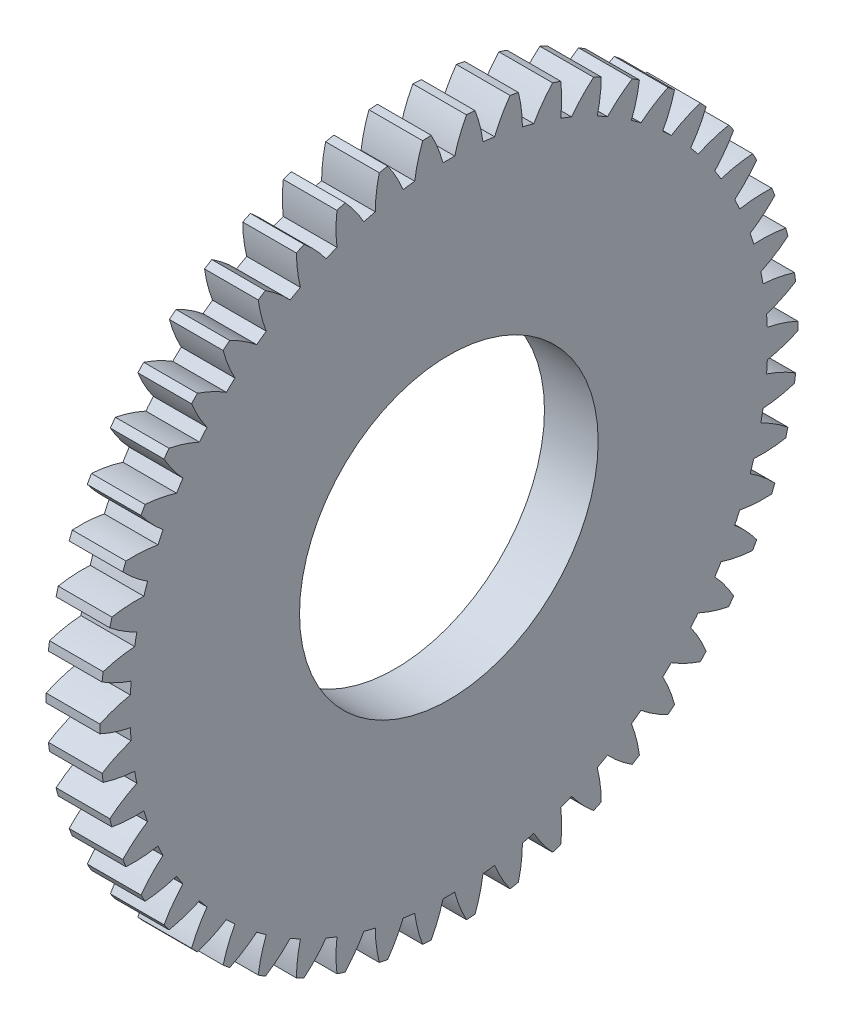
SolidWorks part; units mm, degrees
ref_plane "Plane1" through (0, 0, 0) normal (0, 0, 1) x (1, 0, 0)
ref_plane "Plane2" through (0, 0, 0) normal (0, 1, 0) x (1, 0, 0)
ref_plane "Plane3" through (0, 0, 0) normal (1, 0, 0) x (0, 0, -1)
sketch "HoldingSke" plane through (0, 0, 0) normal (0, 1, 0) x (1, 0, 0)
  line L0 (0, 0) -> (0.6428, -0.766)
  line L1 (-15, 0) -> (100, 0) construction
  line L2 (0, 0) -> (-2.1039, 2.3779)
  line L3 (0, 0) -> (-11.863, 4.5341)
  line L4 (0, 0) -> (5.5511, 6.6156)
  line L5 (0, 0) -> (-46.8476, -17.4728)
  line L6 (0, 0) -> (-3.3159, -2.2372)
  line L7 (-2.1039, 2.3779) -> (8.6586, 51.2059)
  line L8 (-76.2, 54.61) -> (-75.3, 54.61)
  line L9 (-71.009, 38.7566) -> (-53.1078, 45.2721)
  line L10 (-76.2, 71.12) -> (104.1128, 71.12)
  line L11 (0, 0) -> (-4, 0)
  line L12 (-76.2, 101.6) -> (-76.162, 101.6)
  line L13 (24.9733, 27.94) -> (52.9518, 28.4284)
  line L14 (24.9733, 27.94) -> (24.9743, 27.94)
  line L15 (24.9733, 27.94) -> (100.4006, 29.5858)
  line L16 (-63.627, -1) -> (-12.827, -1)
  circle A0 centre (0, 0) radius 2.5
  circle A1 centre (0, 0) radius 23.749
  circle A2 centre (0, 0) radius 37.5
  circle A3 centre (0, 0) radius 2.5
  dimension "MHD" = 47.498
  dimension "Hub_dia" = 75
  dimension "Bore" = 5
  dimension "MBD" = 5
  dimension "Num_teeth" = 50
  dimension "Pitch" = 1
  dimension "Overall_len" = 50
  dimension "Show_teeth" = 50
  dimension "Thickness" = 4
  dimension "OAL" = 50.0001
  dimension "T_dim" = 0.9
  dimension "Ap" = 20
  dimension "H" = 19.05
  dimension "Pitch_radius" = 180.3128
  dimension "Width" = 4
  dimension "Backlash" = 0.038
  dimension "Addendum_fac" = 1
  dimension "Dedendum_fac" = 1.25
  dimension "Clearance_fac" = 0.25
  dimension "Dedendum_add" = 0.001
  dimension "Module" = 1
sketch "BasProSke" plane through (0, 0, 0) normal (0, 1, 0) x (1, 0, 0)
  line L0 (-10, 0) -> (60, 0) construction
  line L1 (0, 0) -> (0, 26)
  line L2 (0, 0) -> (4, 0)
  line L3 (4, 0) -> (4, 26)
  line L4 (4, 26) -> (0, 26)
  dimension "Thickness" = 4
  dimension "Diameter" = 52
revolve "Base-Revolve" add sketch "BasProSke" angle 360 about L0
sketch "TooCutSke" plane through (0, 0, 0) normal (1, 0, 0) x (0, 0, -1)
  line L1 (0, 0) -> (0, 107) construction
  line L2 (0, 0) -> (-0.8518, 24.9855) construction
  line L3 (0, 0) -> (-3.1382, 49.8807) construction
  line L4 (-0.8518, 24.9855) -> (-1.5691, 24.9404) construction
  arc A0 (0.4377, 23.745) -> (-0.4377, 23.745) centre (0, 0) ccw
  arc A1 (1.3294, 25.9914) -> (-1.3294, 25.9914) centre (0, 0) ccw
  circle A2 centre (0, 0) radius 25 construction
  circle A3 centre (0, 0) radius 23.4923 construction
  arc A4 (-0.4377, 23.745) -> (-1.3294, 25.9914) centre (-10.1099, 21.2056) ccw
  arc A5 (1.3294, 25.9914) -> (0.4377, 23.745) centre (10.1099, 21.2056) ccw
  dimension "Root_dia" = 47.498
  dimension "Overcut_dia" = 52.0508
  dimension "Pitch_dia" = 50
  dimension "Base_dia" = 46.9846
  dimension "Flank_rad" = 10
  dimension "Half_ang" = 3.6
  dimension "Half_CT" = 0.7188
extrude "ToothCut" cut sketch "TooCutSke" along normal through all
fillet "Breaks" [suppressed] radius 0.02
fillet "RootFillets" [suppressed] radius 0.251
pattern_circular "TeethCuts" count 50 every 7.2 about axis through (-10, 0, 0) along (1, 0, 0) of "ToothCut", "RootFillets", "Breaks"
sketch "HubNeaOneSke" plane through (0, 0, 0) normal (-1, 0, 0) x (0, 0, 1)
  circle A0 centre (0, 0) radius 23.749
  dimension "Diameter" = 47.498
extrude "HubNearOne" [suppressed] add sketch "HubNeaOneSke" along normal blind 46.0001
sketch "HubNeaBotSke" plane through (0, 0, 0) normal (-1, 0, 0) x (0, 0, 1)
  circle A0 centre (0, 0) radius 23.749
  dimension "Diameter" = 47.498
extrude "HubNearBoth" [suppressed] add sketch "HubNeaBotSke" along normal blind 23
ref_plane "FarPln" through (4, 0, 0) normal (1, 0, 0) x (0, 0, -1)
sketch "HubFarSke" plane through (4, 0, 0) normal (1, 0, 0) x (0, 0, -1)
  circle A0 centre (0, 0) radius 23.749
  dimension "Diameter" = 47.498
extrude "HubFar" [suppressed] add sketch "HubFarSke" along normal blind 23
sketch "BorSke" plane through (0, 0, 0) normal (1, 0, 0) x (0, 0, -1)
  circle A0 centre (0, 0) radius 2.5
  dimension "Diameter" = 5
extrude "Bore" cut sketch "BorSke" along normal mid plane 100.0001
sketch "KeySke" plane through (0, 0, 0) normal (1, 0, 0) x (0, 0, -1)
  line L0 (-1, 0) -> (-1, 3.4)
  line L1 (-1, 3.4) -> (1, 3.4)
  line L2 (1, 3.4) -> (1, 0)
  line L3 (0, 0) -> (0, 34) construction
  line L4 (-1, 0) -> (1, 0)
  dimension "Offset" = 3.4
  dimension "Width" = 2
extrude "Keyway" [suppressed] cut sketch "KeySke" along normal mid plane 100.0001
pattern_circular "Keyway2" [suppressed] count 2 every 90 about axis through (-10, 0, 0) along (1, 0, 0)
sketch "Sketch1" plane through (0, 0, 0) normal (-1, 0, 0) x (0, 0, 1)
  circle A0 centre (0, 0) radius 11.125
  dimension "D1" = 22.25
extrude "Cut-Extrude1" cut sketch "Sketch1" against normal up to next
equation "' \"Module@HoldingSke\" = 6.35"
equation "' \"Num_teeth@HoldingSke\" = 12"
equation "' \"Ap@HoldingSke\" =  20"
equation "' \"Ap@HoldingSke\" = 20"
equation "' \"Width@HoldingSke\" = 0.5 * 25.4"
equation "' \"Hub_dia@HoldingSke\"= 1 * 25.4"
equation "' \"Hub_dia@HoldingSke\" = 1 * 25.4"
equation "' \"Overall_len@HoldingSke\" = 1.0 * 25.4"
equation "' \"Bore@HoldingSke\" = 0.75 * 25.4"
equation "' \"T_dim@HoldingSke\" = 0.1 * 25.4"
equation "' \"Width@KeySke\" = 0.25 * 25.4"
equation "' \"Show_teeth@HoldingSke\" = 13"
equation "' \"Backlash@HoldingSke\" = 0.009 * 25.4"
equation "' \"Addendum_fac@HoldingSke\" = 1.0"
equation "' \"Dedendum_fac@HoldingSke\" = 1.25"
equation "' \"Dedendum_add@HoldingSke\" = 0.00005 * 25.4"
equation "' \"Clearance_fac@HoldingSke\" = 0.25"
equation "\"Pitch@HoldingSke\" = 1 / \"Module@HoldingSke\""
equation "\"Overcut_dia@TooCutSke\" = (\"Num_teeth@HoldingSke\" + 2 * \"Addendum_fac@HoldingSke\") / \"Pitch@HoldingSke\" + 0.002 * 25.4"
equation "\"Pitch_dia@TooCutSke\" = \"Num_teeth@HoldingSke\" / \"Pitch@HoldingSke\""
equation "\"Base_dia@TooCutSke\" = \"Num_teeth@HoldingSke\" / \"Pitch@HoldingSke\" * cos((\"Ap@HoldingSke\"  * 3.14159265 / 180))"
equation "\"Root_dia@TooCutSke\" = (\"Num_teeth@HoldingSke\" + 2) / \"Pitch@HoldingSke\" - 2 * (\"Addendum_fac@HoldingSke\" + \"Dedendum_fac@HoldingSke\") / \"Pitch@HoldingSke\" - \"Dedendum_add@HoldingSke\" * 2"
equation "\"Half_ang@TooCutSke\" = 180 / \"Num_teeth@HoldingSke\""
equation "\"Half_CT@TooCutSke\" = \"Num_teeth@HoldingSke\" / \"Pitch@HoldingSke\" * sin((3.14159265 / 2 / \"Num_teeth@HoldingSke\")) / 2 - 7 * \"Backlash@HoldingSke\" / 4"
equation "\"Flank_rad@TooCutSke\" = \"Num_teeth@HoldingSke\" / \"Pitch@HoldingSke\" / 5"
equation "\"Radius@RootFillets\" = \"Clearance_fac@HoldingSke\" / \"Pitch@HoldingSke\" + \"Dedendum_add@HoldingSke\""
equation "\"Break_rad@Breaks\" = 0.02 / \"Pitch@HoldingSke\""
equation "\"Thickness@HoldingSke\" = \"Width@HoldingSke\""
equation "\"OAL@HoldingSke\" = \"Thickness@HoldingSke\""
equation "\"MHD@HoldingSke\" = (\"Num_teeth@HoldingSke\" + 2) / \"Pitch@HoldingSke\" - 2 * (\"Addendum_fac@HoldingSke\" + \"Dedendum_fac@HoldingSke\")  / \"Pitch@HoldingSke\" - \"Dedendum_add@HoldingSke\" * 2"
equation "\"MBD@HoldingSke\" = (\"Num_teeth@HoldingSke\" + 2) / \"Pitch@HoldingSke\" - 2 * (\"Addendum_fac@HoldingSke\" + \"Dedendum_fac@HoldingSke\")  / \"Pitch@HoldingSke\" - \"Dedendum_add@HoldingSke\" * 2 - 0.002 * 25.4"
equation "\"MHD@HoldingSke\" = ((sgn( \"MHD@HoldingSke\" - \"Hub_dia@HoldingSke\" )-1)*( \"MHD@HoldingSke\" - \"Hub_dia@HoldingSke\" ))/-2+ \"Hub_dia@HoldingSke\""
equation "\"MBD@HoldingSke\" = ((sgn( \"MBD@HoldingSke\" - \"Bore@HoldingSke\" )-1)*( \"MBD@HoldingSke\" - \"Bore@HoldingSke\" ))/-2+ \"Bore@HoldingSke\""
equation "\"OAL@HoldingSke\" = ((sgn( \"OAL@HoldingSke\" - \"Overall_len@HoldingSke\" )+1)*( \"OAL@HoldingSke\" - \"Overall_len@HoldingSke\" ))/2 + \"Overall_len@HoldingSke\" + 0.000002 * 25.4"
equation "\"Num_teeth@TeethCuts\" = int( \"Show_teeth@HoldingSke\" ) + 1"
equation "\"Num_teeth@TeethCuts\" = ((sgn( \"Num_teeth@TeethCuts\" - \"Num_teeth@HoldingSke\" )-1)*( \"Num_teeth@TeethCuts\" - \"Num_teeth@HoldingSke\" ))/-2+ \"Num_teeth@HoldingSke\""
equation "\"Num_teeth@TeethCuts\" = ((sgn( \"Num_teeth@TeethCuts\" - 2.0)+1)*( \"Num_teeth@TeethCuts\" - 2.0))/2 +2.0"
equation "\"Angle@TeethCuts\" = 360.0 / \"Num_teeth@HoldingSke\""
equation "\"Diameter@BasProSke\" = (\"Num_teeth@HoldingSke\" + 2 * \"Addendum_fac@HoldingSke\") / \"Pitch@HoldingSke\""
equation "\"Thickness@BasProSke\"  = \"Thickness@HoldingSke\""
equation "' \"Fillet_rad@BasProSke\" =  \"Thickness@HoldingSke\" * 0.05"
equation "' \"Fillet_rad@BasProSke\" = \"Thickness@HoldingSke\" * 0.05"
equation "\"MHD@HoldingSke\" = ((sgn( \"MHD@HoldingSke\" - \"Root_dia@TooCutSke\" )-1)*( \"MHD@HoldingSke\" - \"Root_dia@TooCutSke\" ))/-2+ \"Root_dia@TooCutSke\""
equation "\"Diameter@HubNeaOneSke\" = \"MHD@HoldingSke\""
equation "\"Length@HubNearOne\" = \"OAL@HoldingSke\" - \"Thickness@BasProSke\""
equation "\"Diameter@HubNeaBotSke\" = \"MHD@HoldingSke\""
equation "\"Length@HubNearBoth\" = ( \"OAL@HoldingSke\" - \"Thickness@BasProSke\" ) / 2.0"
equation "\"Thickness@FarPln\" = \"Thickness@BasProSke\""
equation "\"Diameter@HubFarSke\" = \"MHD@HoldingSke\""
equation "\"Length@HubFar\" = ( \"OAL@HoldingSke\" - \"Thickness@BasProSke\" ) / 2.0"
equation "\"Diameter@BorSke\" = \"MBD@HoldingSke\""
equation "\"D1@Bore\" = \"OAL@HoldingSke\" * 2.0"
equation "\"D1@Keyway\" = \"OAL@HoldingSke\" * 2.0"
equation "\"Offset@KeySke\" = \"T_dim@HoldingSke\" + \"MBD@HoldingSke\" / 2.0"
